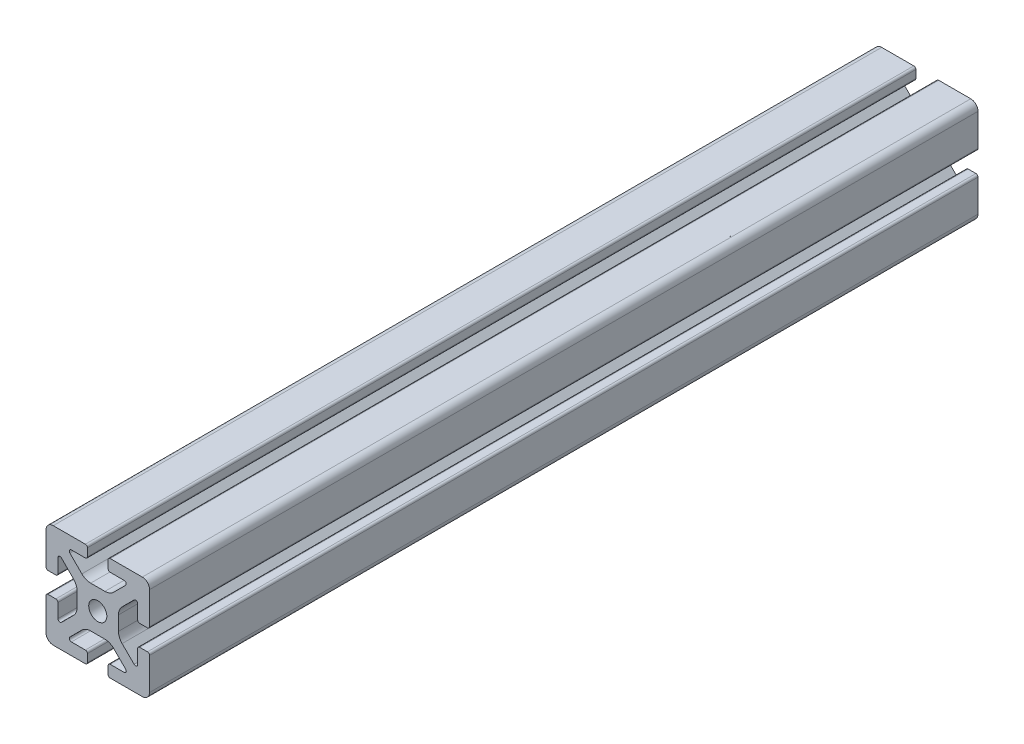
SolidWorks part; units mm, degrees
material "6061-T6 (SS)"
ref_plane "Front Plane" through (0, 0, 0) normal (0, 0, 1) x (1, 0, 0)
ref_plane "Top Plane" through (0, 0, 0) normal (0, 1, 0) x (1, 0, 0)
ref_plane "Right Plane" through (0, 0, 0) normal (1, 0, 0) x (0, 0, -1)
sketch "Sketch2" plane through (0, 0, 0) normal (0, 0, 1) x (1, 0, 0)
  line L0 (0, 20) -> (0, -20) construction
  line L1 (-20, 0) -> (20, 0) construction
  line L2 (4, -20) -> (20, -20)
  line L3 (20, -20) -> (20, -4)
  line L4 (4, -20) -> (4, -15.3907)
  line L5 (4, -15.3907) -> (12.1314, -15.3907)
  line L6 (12.1314, -15.3907) -> (4.7407, -8)
  line L7 (0, 0) -> (20, -20) construction
  line L8 (20, -4) -> (15.3907, -4)
  line L9 (15.3907, -4) -> (15.3907, -12.1314)
  line L10 (15.3907, -12.1314) -> (8, -4.7407)
  line L11 (11.6953, -8.436) -> (8.436, -11.6953) construction
  circle A0 centre (0, 0) radius 3.5
  arc A1 (10.2, -15.3907) -> (10.7657, -14.025) centre (10.2, -14.5907) ccw construction
  point P8 (0, -8)
  point P16 (10.0657, -10.0657)
  dimension "Center Hole Diameter" = 7
  dimension "D3" = 0.8
  dimension "Rail Height" = 40
  dimension "Rail Width" = 40
  dimension "T-Slot Width" = 8
  dimension "Slot Depth" = 12
  dimension "Slot Inner Width" = 22
sketch "Sketch3" plane through (0, 0, 0) normal (1, 0, 0) x (0, 0, -1)
  line L0 (-457.2, -20) -> (457.2, -20) construction
  line L1 (-431.8, 0) -> (431.8, 0) construction
  line L2 (0, 20) -> (0, -20) construction
  line L3 (0, 20) -> (0, -20) construction
  point P6 (-431.8, 0)
  point P8 (431.8, 0)
  dimension "Length" = 914.4
  dimension "D1" = 25.4
sketch "Sketch4" plane through (0, 0, 0) normal (0, 0, 1) x (1, 0, 0)
  line L0 (4.8, -20) -> (17.2, -20)
  line L1 (4, -20) -> (20, -20) construction
  line L2 (4, -20) -> (4, -15.3907) construction
  line L3 (4, -15.3907) -> (12.1314, -15.3907) construction
  line L4 (4, -16.1907) -> (4, -19.2)
  line L5 (4.8, -15.3907) -> (10.2, -15.3907)
  line L6 (0, -8) -> (2.7525, -8)
  line L7 (12.1314, -15.3907) -> (4.7407, -8) construction
  line L8 (6.1466, -9.4059) -> (10.7657, -14.025)
  line L9 (20, -20) -> (20, -4) construction
  line L10 (15.3907, -12.1314) -> (8, -4.7407) construction
  line L11 (15.3907, -4) -> (15.3907, -12.1314) construction
  line L12 (15.3907, -10.2) -> (15.3907, -4.8)
  line L13 (20, -4) -> (15.3907, -4) construction
  line L14 (16.1907, -4) -> (19.2, -4)
  line L15 (20, -4.8) -> (20, -17.2)
  line L16 (14.025, -10.7657) -> (9.4059, -6.1466)
  line L17 (8, 0) -> (8, -2.7525)
  line L18 (-20, 0) -> (20, 0) construction
  line L19 (0, -8) -> (0, -3.5)
  line L20 (0, 20) -> (0, -20) construction
  line L21 (8, 0) -> (3.5, 0)
  arc A0 (4, -19.2) -> (4.8, -20) centre (4.8, -19.2) ccw
  arc A1 (10.2, -15.3907) -> (10.7657, -14.025) centre (10.2, -14.5907) ccw construction
  arc A2 (4, -16.1907) -> (4.8, -15.3907) centre (4.8, -16.1907) cw
  arc A3 (10.2, -15.3907) -> (10.7657, -14.025) centre (10.2, -14.5907) ccw
  arc A4 (2.7525, -8) -> (6.1466, -9.4059) centre (2.7525, -12.8) cw
  arc A5 (17.2, -20) -> (20, -17.2) centre (17.2, -17.2) ccw
  arc A6 (14.025, -10.7657) -> (15.3907, -10.2) centre (14.5907, -10.2) ccw
  arc A7 (15.3907, -4.8) -> (16.1907, -4) centre (16.1907, -4.8) cw
  arc A8 (19.2, -4) -> (20, -4.8) centre (19.2, -4.8) cw
  arc A9 (9.4059, -6.1466) -> (8, -2.7525) centre (12.8, -2.7525) cw
  circle A10 centre (0, 0) radius 3.5 construction
  arc A11 (0, -3.5) -> (3.5, 0) centre (0, 0) ccw
  dimension "D1" = 2.8
  dimension "D2" = 4.8
extrude "Boss-Extrude1" add sketch "Sketch4" along normal mid plane 320
mirror "Mirror1" about plane through (0, 0, 0) normal (1, 0, 0) of bodies 134
mirror "Mirror2" about plane through (0, 0, 0) normal (0, 1, 0) of bodies 135
equation "\"D3@Sketch2\"=\"T-Slot Width@Sketch2\"*0.1"
equation "\"D1@Sketch4\"=\"D3@Sketch2\"*3.5"
equation "\"D2@Sketch4\"=\"D3@Sketch2\"*6"
equation "\"D1@Boss-Extrude1\"=\"Length@Sketch3\""
